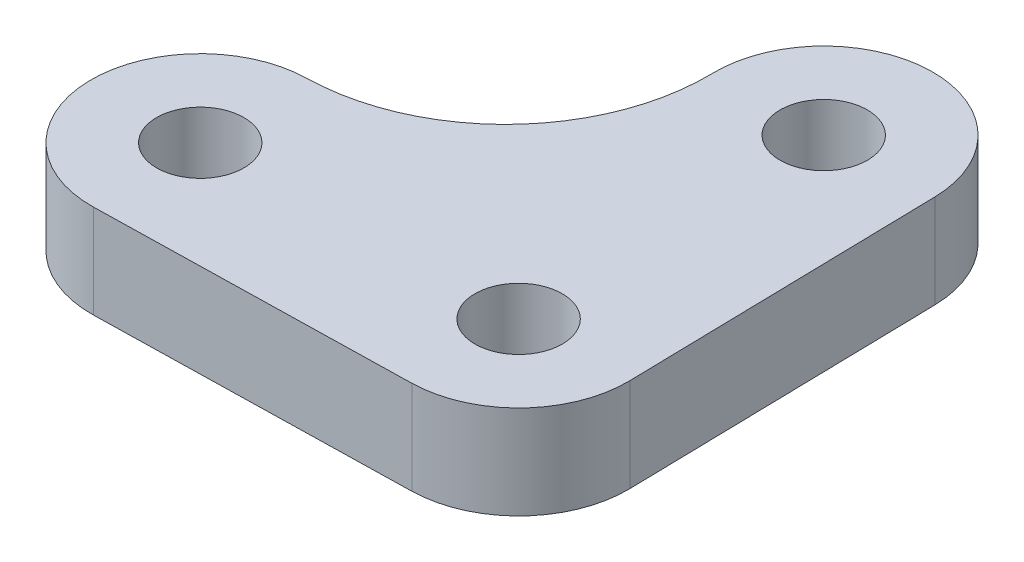
SolidWorks part; units mm, degrees
ref_plane "Front Plane" through (0, 0, 0) normal (0, 0, 1) x (1, 0, 0)
ref_plane "Top Plane" through (0, 0, 0) normal (0, 1, 0) x (1, 0, 0)
ref_plane "Right Plane" through (0, 0, 0) normal (1, 0, 0) x (0, 0, -1)
sketch "Sketch1" plane through (0, 0, 0) normal (0, 1, 0) x (1, 0, 0)
  line L0 (8.4981, -4.8185) -> (8.2858, 5.1793)
  line L1 (-4.9246, -8.6042) -> (5.0732, -8.392)
  circle A0 centre (4.7866, 5.105) radius 1.4
  arc A1 (8.2858, 5.1793) -> (1.2874, 5.0307) centre (4.7866, 5.105) ccw
  arc A2 (-5.0732, -1.6058) -> (1.2874, 5.0307) centre (-5.2111, 4.8927) ccw
  arc A3 (-5.0732, -1.6058) -> (-4.9246, -8.6042) centre (-4.9989, -5.105) ccw
  arc A4 (5.0732, -8.392) -> (8.4981, -4.8185) centre (4.9989, -4.8927) ccw
  circle A5 centre (4.9989, -4.8927) radius 1.4
  circle A6 centre (-4.9989, -5.105) radius 1.4
  dimension "D2" = 2.8
  dimension "D3" = 2.8
  dimension "D4" = 2.8
  dimension "D1" = 9.9977
extrude "Boss-Extrude1" add sketch "Sketch1" along normal blind 3
